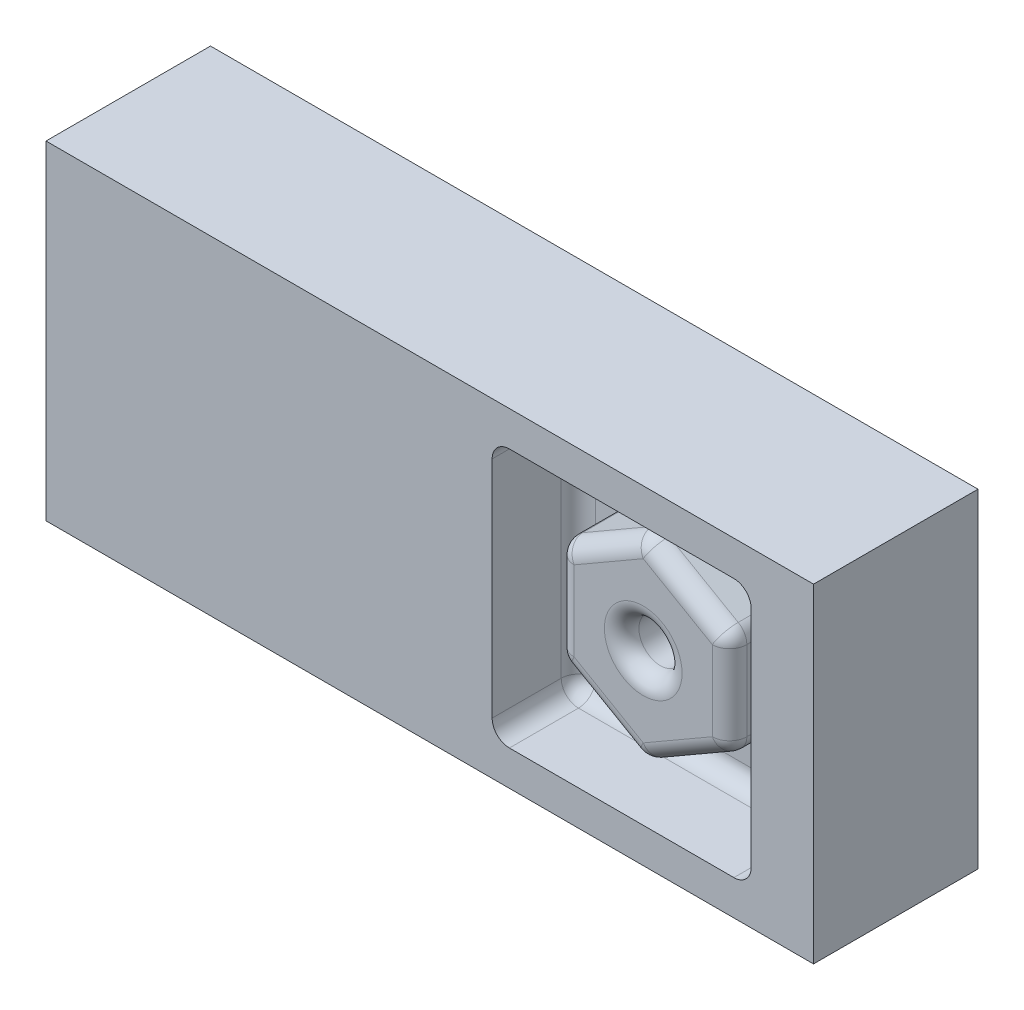
SolidWorks part; units mm, degrees
ref_plane "Alzado" through (0, 0, 0) normal (0, 0, 1) x (1, 0, 0)
ref_plane "Planta" through (0, 0, 0) normal (0, 1, 0) x (1, 0, 0)
ref_plane "Vista lateral" through (0, 0, 0) normal (1, 0, 0) x (0, 0, -1)
sketch "Croquis1" plane through (0, 0, 0) normal (0, 0, 1) x (1, 0, 0)
  line L1 (88.9, -38.1) -> (-88.9, -38.1)
  line L2 (88.9, -38.1) -> (88.9, 38.1)
  line L3 (88.9, 38.1) -> (-88.9, 38.1)
  line L4 (-88.9, -38.1) -> (-88.9, 38.1)
  line L5 (88.9, -38.1) -> (-88.9, 38.1) construction
  line L6 (88.9, 38.1) -> (-88.9, -38.1) construction
  point P0 (0, 0)
  dimension "D1" = 177.8
  dimension "D2" = 76.2
extrude "Saliente-Extruir1" add sketch "Croquis1" along normal blind 38.1
sketch "Croquis2" plane through (0, 0, 38.1) normal (0, 0, 1) x (1, 0, 0)
  line L0 (88.9, 38.1) -> (0, -38.1) construction
  line L1 (-88.9, -38.1) -> (88.9, -38.1) construction
  line L3 (74.45, -30) -> (14.45, -30)
  line L4 (74.45, -30) -> (74.45, 30)
  line L5 (74.45, 30) -> (14.45, 30)
  line L6 (14.45, -30) -> (14.45, 30)
  line L7 (74.45, -30) -> (14.45, 30) construction
  line L8 (74.45, 30) -> (14.45, -30) construction
  point P5 (44.45, 0)
  dimension "D1" = 60
  dimension "D2" = 60
extrude "Cortar-Extruir1" cut sketch "Croquis2" against normal blind 20
sketch "Croquis3" plane through (0, 0, 18.1) normal (0, 0, 1) x (1, 0, 0)
  line L0 (14.45, 30) -> (74.45, -30) construction
  line L2 (44.45, 23.094) -> (24.45, 11.547)
  line L3 (24.45, 11.547) -> (24.45, -11.547)
  line L4 (24.45, -11.547) -> (44.45, -23.094)
  line L5 (44.45, -23.094) -> (64.45, -11.547)
  line L6 (64.45, -11.547) -> (64.45, 11.547)
  line L7 (64.45, 11.547) -> (44.45, 23.094)
  circle A0 centre (44.45, 0) radius 20 construction
  circle A1 centre (44.45, 0) radius 5
  dimension "D1" = 40
  dimension "D2" = 10
extrude "Saliente-Extruir2" add sketch "Croquis3" along normal blind 15
fillet "Redondeo1" radius 4 8 edges at (74.45, -30, 28.1) (14.45, -30, 28.1) (14.45, 30, 28.1) (74.45, 30, 28.1) (74.45, 0, 18.1) (44.45, -30, 18.1) (14.45, 0, 18.1) (44.45, 30, 18.1)
fillet "Redondeo3" radius 4 6 edges at (64.45, 11.547, 25.6) (64.45, -11.547, 25.6) (44.45, -23.094, 25.6) (24.45, -11.547, 25.6) (24.45, 11.547, 25.6) (44.45, 23.094, 25.6)
fillet "Redondeo4" radius 4 1 edges at (49.45, 0, 33.1)
fillet "Redondeo5" radius 4 12 edges at (24.9859, 11.2376, 33.1) (34.45, 17.3205, 33.1) (44.45, 22.4752, 33.1) (54.45, 17.3205, 33.1) (63.9141, 11.2376, 33.1) (64.45, 0, 33.1) (63.9141, -11.2376, 33.1) (54.45, -17.3205, 33.1) (44.45, -22.4752, 33.1) (34.45, -17.3205, 33.1) (24.9859, -11.2376, 33.1) (24.45, 0, 33.1)
